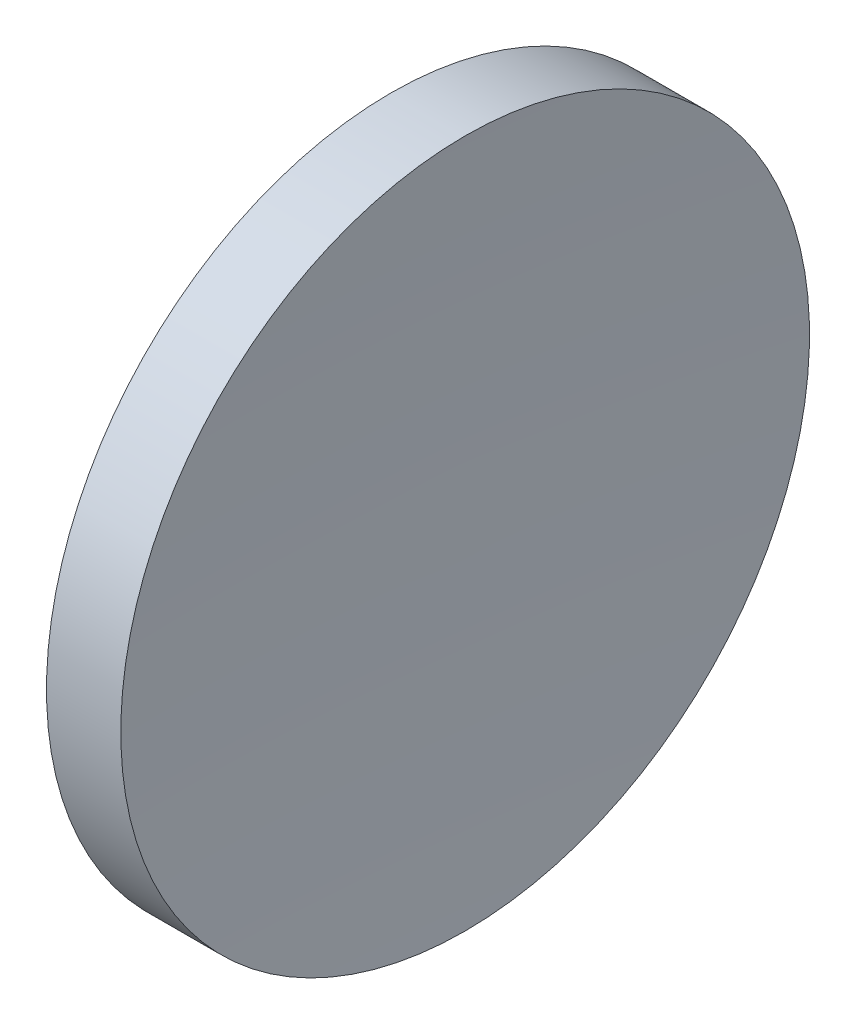
SolidWorks part; units mm, degrees
ref_plane "前视基准面" through (0, 0, 0) normal (0, 0, 1) x (1, 0, 0)
ref_plane "上视基准面" through (0, 0, 0) normal (0, 1, 0) x (1, 0, 0)
ref_plane "右视基准面" through (0, 0, 0) normal (1, 0, 0) x (0, 0, -1)
sketch "草图1" plane through (0, 0, 0) normal (0, 0, 1) x (1, 0, 0)
  line L0 (89.8587, 52.1781) -> (104.0854, 52.1781) construction
  line L1 (97.0904, 52.1781) -> (95.0904, 52.1781)
  line L3 (96.0904, 64.8781) -> (97.4603, 64.8781)
  line L4 (96.0904, 64.8781) -> (94.7206, 64.8781)
  arc A0 (95.0904, 52.1781) -> (94.7206, 64.8781) centre (-115.9095, 52.3884) ccw
  arc A1 (97.4603, 64.8781) -> (97.0904, 52.1781) centre (308.0903, 52.3884) ccw
revolve "旋转1" add sketch "草图1" angle 360 about L0
